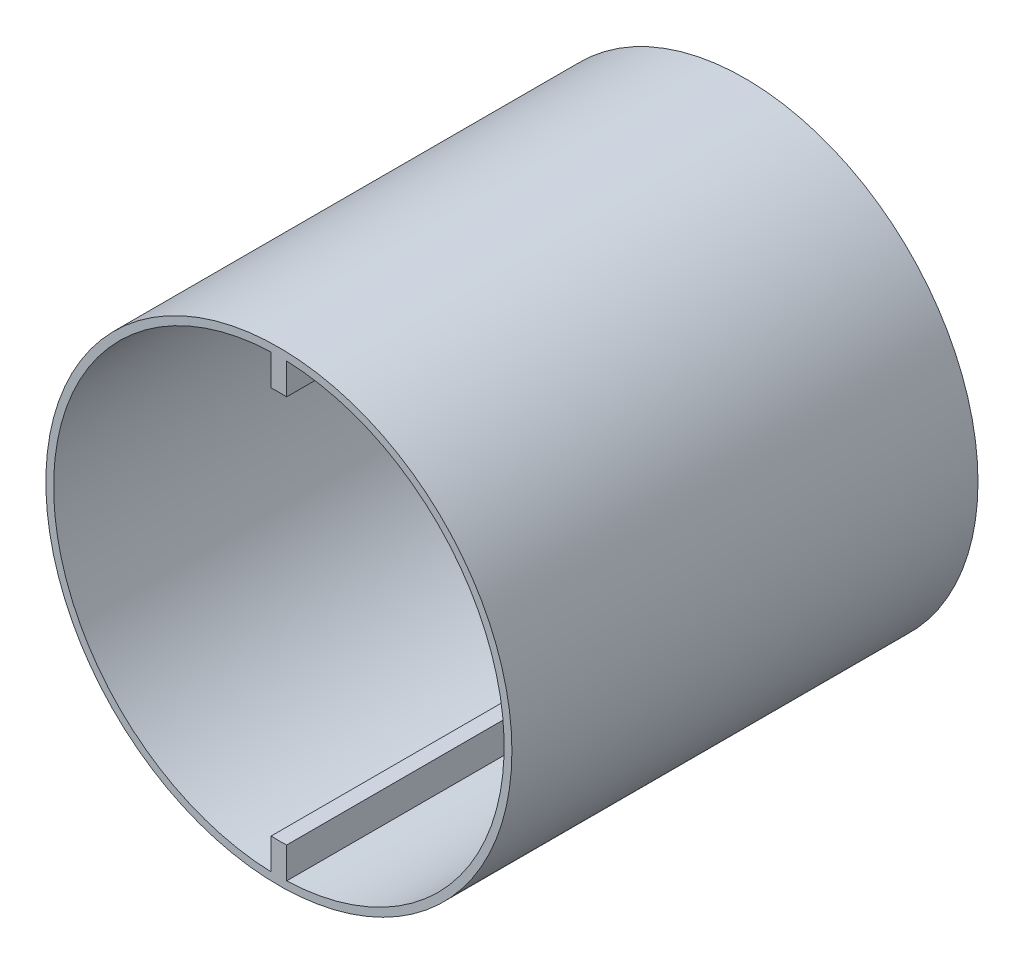
SolidWorks part; units mm, degrees
ref_plane "Plan de face" through (0, 0, 0) normal (0, 0, 1) x (1, 0, 0)
ref_plane "Plan de dessus" through (0, 0, 0) normal (0, 1, 0) x (1, 0, 0)
ref_plane "Plan de droite" through (0, 0, 0) normal (1, 0, 0) x (0, 0, -1)
sketch "Esquisse1" plane through (0, 0, 0) normal (0, 0, 1) x (1, 0, 0)
  line L0 (1, -15.0065) -> (1, -3.3541)
  line L1 (1, 29.5) -> (-1, 29.5)
  line L2 (-1, 29.5) -> (-1, 3.3541)
  line L3 (-1, -29.5) -> (1, -29.5)
  line L4 (1, -29.5) -> (1, -15.0065)
  line L5 (-1, -3.3541) -> (-1, -29.5)
  line L6 (1, 3.3541) -> (1, 29.5)
  arc A0 (-1, 3.3541) -> (-1, -3.3541) centre (0, 0) ccw
  arc A1 (1, -3.3541) -> (1, 3.3541) centre (0, 0) ccw
  dimension "D1" = 7
  dimension "D6" = 15.0065
  dimension "D2" = 59
  dimension "D3" = 29.5
  dimension "D4" = 2
  dimension "D5" = 1
extrude "Boss.-Extru.1" add sketch "Esquisse1" along normal blind 60
sketch "Esquisse2" plane through (0, 0, 60) normal (0, 0, 1) x (1, 0, 0)
  circle A0 centre (0, 0) radius 30
  circle A1 centre (0, 0) radius 29
  dimension "D1" = 60
  dimension "D2" = 58
extrude "Boss.-Extru.2" add sketch "Esquisse2" against normal blind 60
sketch "Esquisse3" plane through (0, 0, 60) normal (0, 0, 1) x (1, 0, 0)
  circle A0 centre (0, 0) radius 25
  dimension "D1" = 50
extrude "Enlèv. mat.-Extru.1" cut sketch "Esquisse3" against normal blind 27
sketch "Esquisse4" plane through (-1, 0, 0) normal (-1, 0, 0) x (0, 0, 1)
sketch "Esquisse6" plane through (0, 0, 33) normal (0, 0, 1) x (1, 0, 0)
  circle A0 centre (0, 0) radius 2.225
  dimension "D1" = 4.45
extrude "Enlèv. mat.-Extru.3" cut sketch "Esquisse6" against normal blind 2
sketch "Esquisse11" plane through (0, 0, 60) normal (0, 0, 1) x (1, 0, 0)
  circle A0 centre (0, 0) radius 25
  circle A1 centre (0, 0) radius 3.5
  dimension "D1" = 7
extrude "Enlèv. mat.-Extru.8" cut sketch "Esquisse11" against normal blind 31
sketch "Esquisse12" plane through (0, 0, 0) normal (0, 0, -1) x (-1, 0, 0)
  circle A0 centre (0, 0) radius 28.9828
  circle A1 centre (0, 0) radius 14.3748
  dimension "D1" = 57.9655
